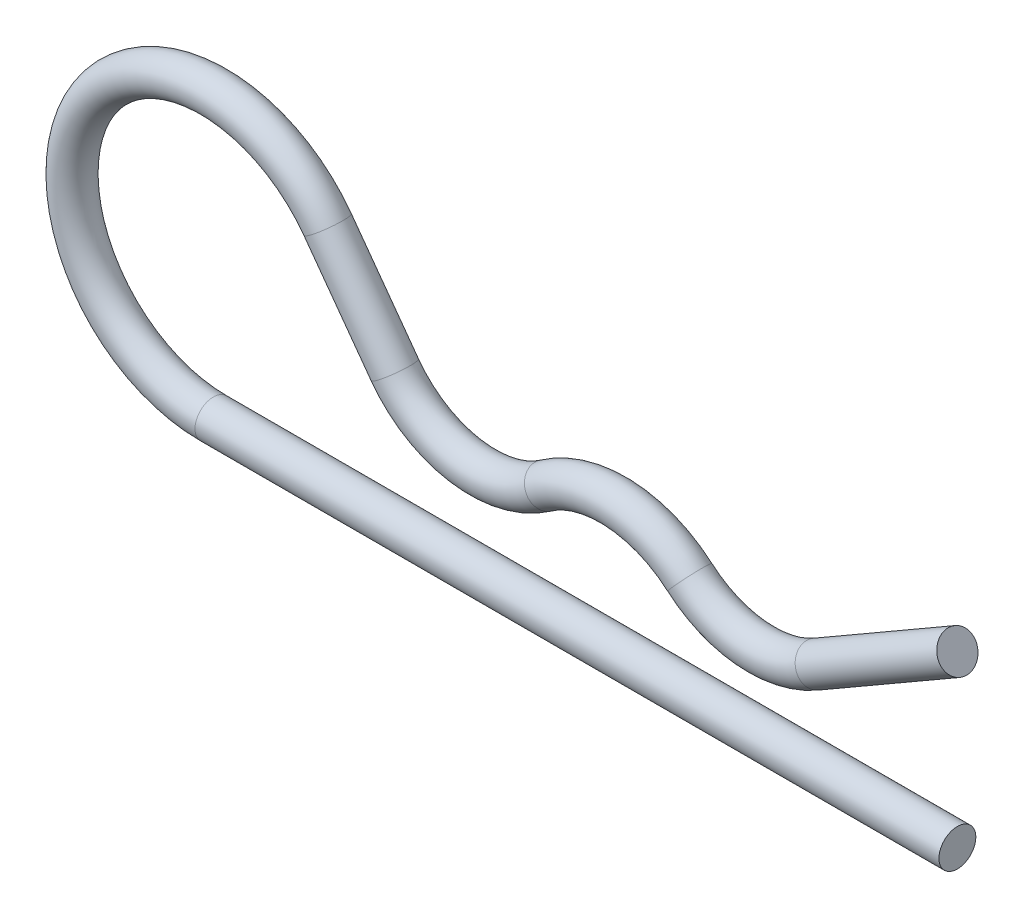
SolidWorks part; units mm, degrees
ref_plane "Płaszczyzna przednia" through (0, 0, 0) normal (0, 0, 1) x (1, 0, 0)
ref_plane "Płaszczyzna górna" through (0, 0, 0) normal (0, 1, 0) x (1, 0, 0)
ref_plane "Płaszczyzna prawa" through (0, 0, 0) normal (1, 0, 0) x (0, 0, -1)
sketch "Szkic1" plane through (0, 0, 0) normal (0, 0, 1) x (1, 0, 0)
  line L0 (0, -11.5) -> (60.5, -11.5)
  line L1 (9.294, 6.7728) -> (14.7542, -0.72)
  line L3 (48.9867, -4.3289) -> (60.5, 2.3183)
  line L4 (60.5, 2.3183) -> (60.5, -11.5) construction
  arc A0 (9.294, 6.7728) -> (0, -11.5) centre (0, 0) ccw
  arc A1 (38.7401, -3.3368) -> (27.0209, -2.7392) centre (32.5, -10.5) ccw
  arc A2 (38.7401, -3.3368) -> (48.9867, -4.3289) centre (44.558, 3.3417) ccw
  arc A3 (14.7542, -0.72) -> (27.0209, -2.7392) centre (21.9125, 4.4965) ccw
  point P13 (32.5, -9.6744)
  dimension "D1" = 11.5
  dimension "D2" = 9.5
  dimension "D3" = 1
  dimension "D5" = 60.5
  dimension "D6" = 32.5
  dimension "D4" = 30
  dimension "D7" = 28
ref_plane "Płaszczyzna1" through (60.5, -11.5, 0) normal (1, 0, 0) x (0, 0, -1)
sketch "Szkic2" plane through (60.5, -11.5, 0) normal (1, 0, 0) x (0, 0, -1)
  circle A0 centre (0, 0) radius 1.5
sweep "Wyciągnięcie po ścieżce1" add profiles "Szkic2" path "Szkic1"
